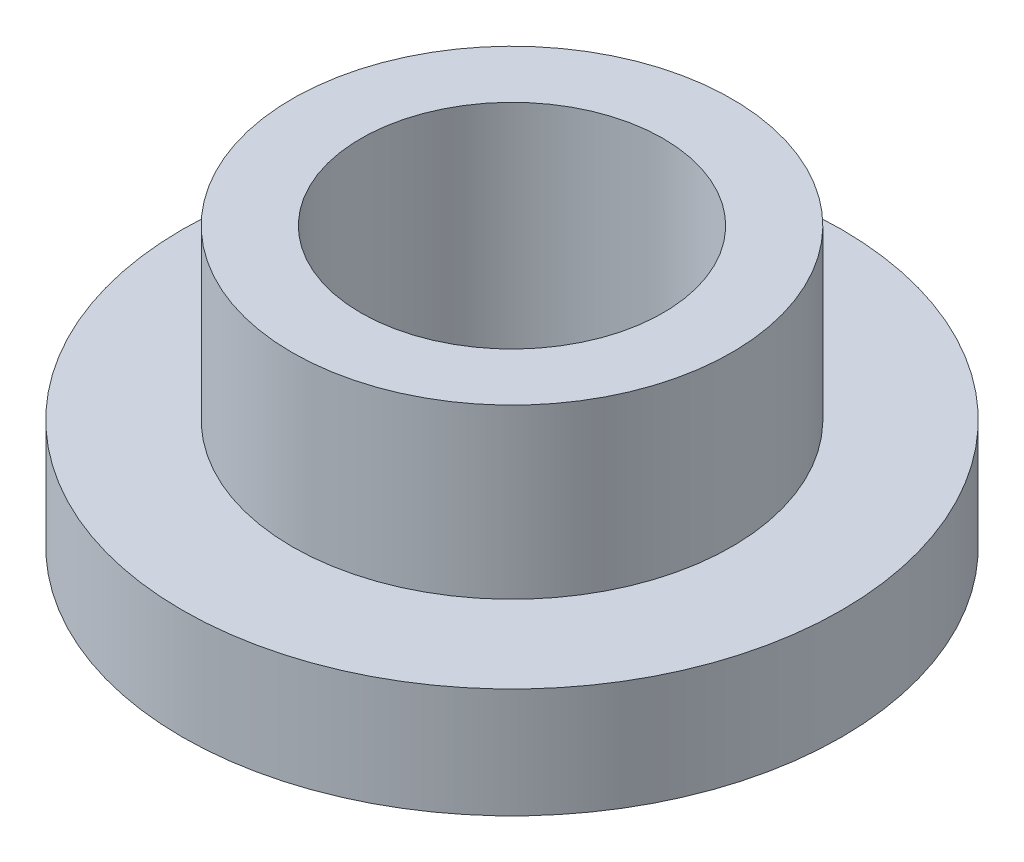
SolidWorks part; units mm, degrees
ref_plane "Front Plane" through (0, 0, 0) normal (0, 0, 1) x (1, 0, 0)
ref_plane "Top Plane" through (0, 0, 0) normal (0, 1, 0) x (1, 0, 0)
ref_plane "Right Plane" through (0, 0, 0) normal (1, 0, 0) x (0, 0, -1)
sketch "Sketch1" plane through (0, 0, 0) normal (0, 1, 0) x (1, 0, 0)
  circle A0 centre (0, 0) radius 2.1828
  circle A1 centre (0, 0) radius 4.7625
  dimension "D1" = 9.525
  dimension "D2" = 4.3656
extrude "Boss-Extrude1" add sketch "Sketch1" along normal blind 1.5875
sketch "Sketch2" plane through (0, 1.5875, 0) normal (0, 1, 0) x (1, 0, 0)
  circle A0 centre (0, 0) radius 2.1828
  circle A1 centre (0, 0) radius 3.175
  dimension "D1" = 4.3656
  dimension "D2" = 6.35
extrude "Boss-Extrude2" add sketch "Sketch2" along normal blind 2.4289
